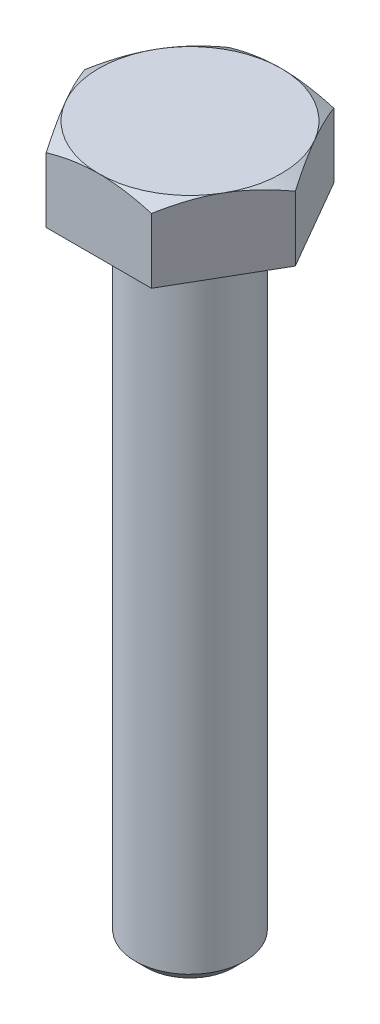
SolidWorks part; units mm, degrees
ref_plane "Plan1" through (0, 0, 0) normal (0, 0, 1) x (1, 0, 0)
ref_plane "Plan2" through (0, 0, 0) normal (0, 1, 0) x (1, 0, 0)
ref_plane "Plan3" through (0, 0, 0) normal (1, 0, 0) x (0, 0, -1)
sketch "Esquisse2" plane through (0, 0, 0) normal (0, 1, 0) x (1, 0, 0)
  circle A0 centre (0, 0) radius 3
  dimension "Diamètre nominal" = 6
extrude "Base-Extrusion" add sketch "Esquisse2" against normal blind 35
chamfer "Chanfrein1" distance 0.6 angle 45
sketch "Esquisse5" plane through (0, 0, 0) normal (0, 0, 1) x (1, 0, 0)
  line L0 (-5, 0) -> (5, 0) construction
  line L1 (0, 0) -> (7.0711, 0)
  line L2 (0, 0) -> (0, 4)
  line L3 (0, 4) -> (5, 4)
  line L5 (7.0711, 0) -> (7.0711, 2.8043)
  line L6 (5, 4) -> (7.0711, 2.8043)
  line L7 (0, 4) -> (0, -35) construction
  line L8 (0, -34.4) -> (0, 0) construction
  line L9 (-2.4, -35) -> (2.4, -35) construction
  dimension "D1" = 7.0711
  dimension "Hauteur tête" = 4
  dimension "Cote sur plats" = 10
  dimension "D3" = 30
  dimension "D4" = 5
revolve "Boss.-Révol.1" add sketch "Esquisse5" angle 360 about L7
sketch "Esquisse6" plane through (0, 0, 0) normal (0, -1, 0) x (1, 0, 0)
  line L0 (5.7735, 0) -> (-5, 0) construction
  line L1 (0, 0) -> (3.5355, -6.1237) construction
  line L2 (0, 0) -> (6.1237, -3.5355) construction
  line L3 (0, 0) -> (0, -5) construction
  line L4 (-2.8868, -5) -> (2.8868, -5)
  line L5 (2.8868, -5) -> (5.7735, 0)
  line L6 (-2.8868, 5) -> (2.8868, 5)
  line L7 (2.8868, 5) -> (5.7735, 0)
  line L8 (-2.8868, -5) -> (-5.7735, 0)
  line L9 (-2.8868, 5) -> (-5.7735, 0)
  circle A0 centre (0, 0) radius 7.0711 construction
  circle A3 centre (0, 0) radius 5 construction
  point P17 (0, 5)
  dimension "D1" = 30
  dimension "D2" = 30
extrude "Enlèv. mat.-Extru.1" cut sketch "Esquisse6" against normal blind 4 flip side to cut
sketch "Esquisse3" plane through (0, -35, 0) normal (0, -1, 0) x (1, 0, 0)
  circle A0 centre (0, 0) radius 3
  circle A1 centre (0, 0) radius 3 construction
equation "\"D4@Esquisse5\" = \"Cote sur plats@Esquisse5\"/2"
equation "\"D1@Esquisse5\" =(\"D4@Esquisse5\"*sqr(2)*2)/2"
equation "\"D1@Chanfrein1\" = \"Diamètre nominal@Esquisse2\"*0.1"
